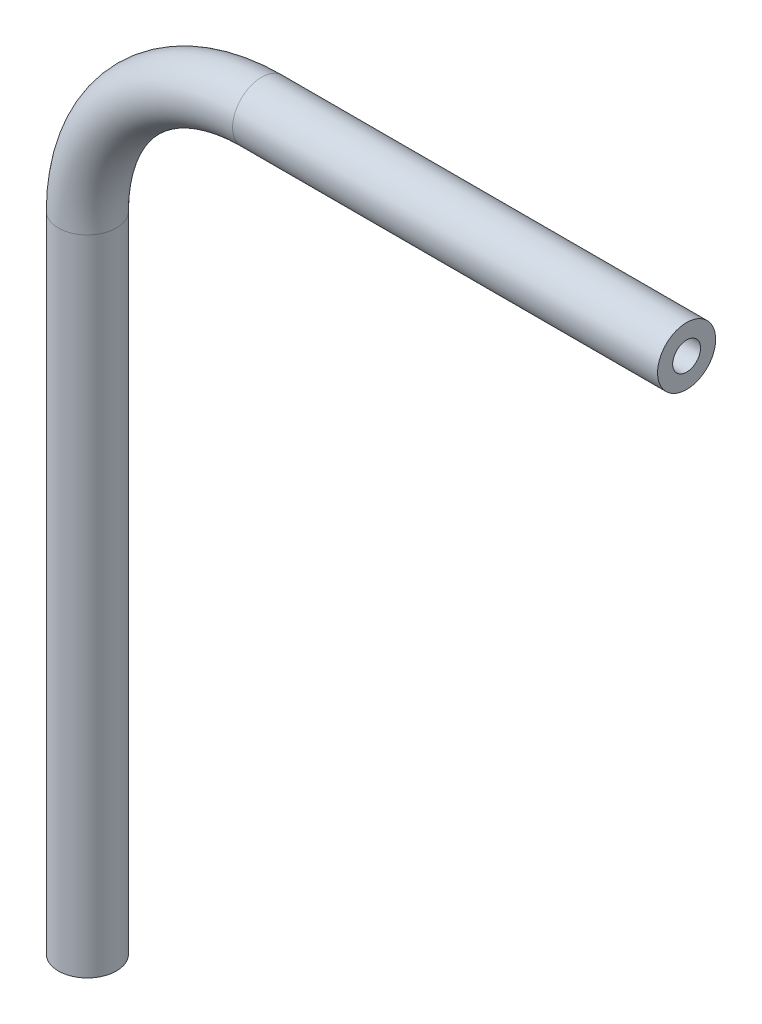
SolidWorks part; units mm, degrees
material "AISI Type 316L stainless steel"
ref_plane "Front Plane" through (0, 0, 0) normal (0, 0, 1) x (1, 0, 0)
ref_plane "Top Plane" through (0, 0, 0) normal (0, 1, 0) x (1, 0, 0)
ref_plane "Right Plane" through (0, 0, 0) normal (1, 0, 0) x (0, 0, -1)
sketch "Sketch1" plane through (0, 0, 0) normal (0, 0, 1) x (1, 0, 0)
  line L0 (0, -71.8803) -> (0, -1.5223)
  line L1 (19.05, 17.5277) -> (65.5179, 17.5277)
  arc A0 (0, -1.5223) -> (19.05, 17.5277) centre (19.05, -1.5223) cw
  point P6 (0, 17.5277)
  dimension "D3" = 19.05
  dimension "D1" = 65.5179
  dimension "D2" = 89.408
  dimension "D4" = 90
ref_plane "Plane1" through (65.5179, 17.5277, 0) normal (1, 0, 0) x (0, 0, -1)
sketch "Sketch2" plane through (65.5179, 17.5277, 0) normal (1, 0, 0) x (0, 0, -1)
  circle A0 centre (0, 0) radius 3.175
  circle A1 centre (0, 0) radius 1.524
  dimension "D1" = 6.35
  dimension "D2" = 3.048
sweep "Sweep1" add profiles "Sketch2" path "Sketch1"
